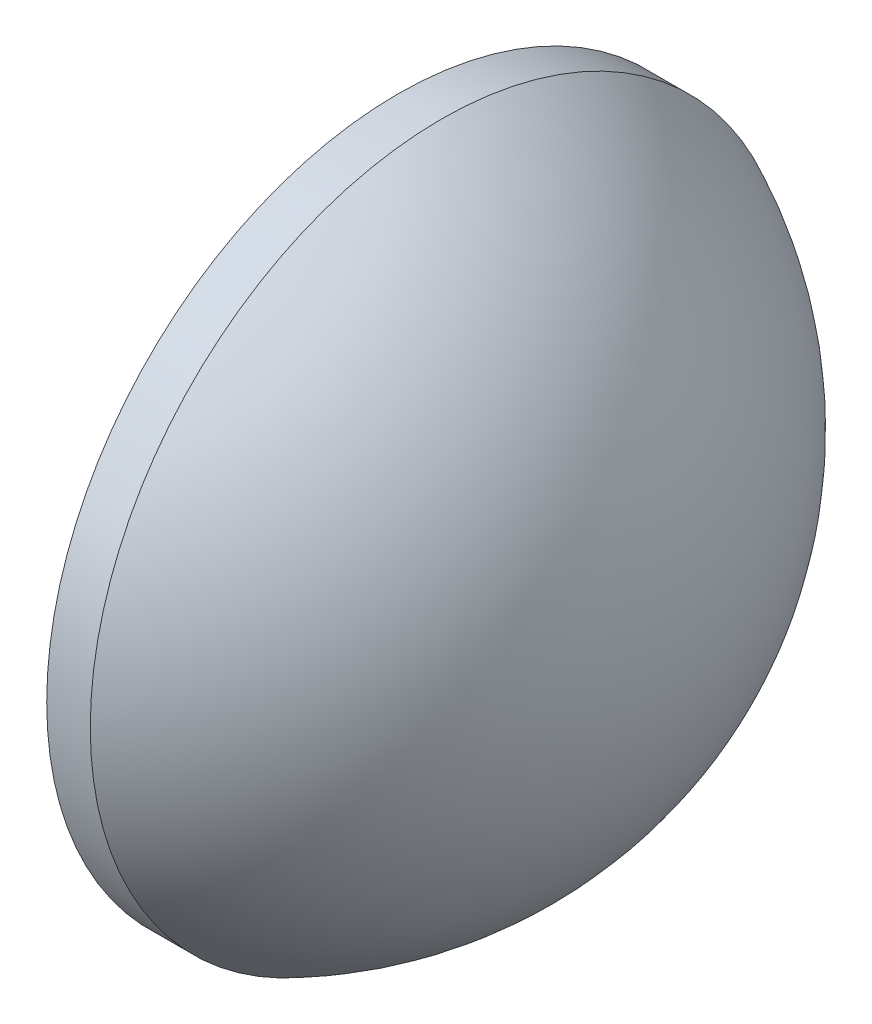
SolidWorks part; units mm, degrees
ref_plane "前视基准面" through (0, 0, 0) normal (0, 0, 1) x (1, 0, 0)
ref_plane "上视基准面" through (0, 0, 0) normal (0, 1, 0) x (1, 0, 0)
ref_plane "右视基准面" through (0, 0, 0) normal (1, 0, 0) x (0, 0, -1)
sketch "草图1" plane through (0, 0, 0) normal (0, 0, 1) x (1, 0, 0)
  line L0 (486.8548, 171.7157) -> (500.3006, 171.7157) construction
  line L1 (488.3669, 171.7157) -> (488.3669, 184.2157)
  line L2 (497.8669, 171.7157) -> (488.3669, 171.7157)
  line L5 (488.3669, 184.2157) -> (489.9169, 184.2157)
  arc A0 (497.8669, 171.7157) -> (489.9169, 184.2157) centre (484.0648, 171.7157) ccw
revolve "旋转1" add sketch "草图1" angle 360 about L0
